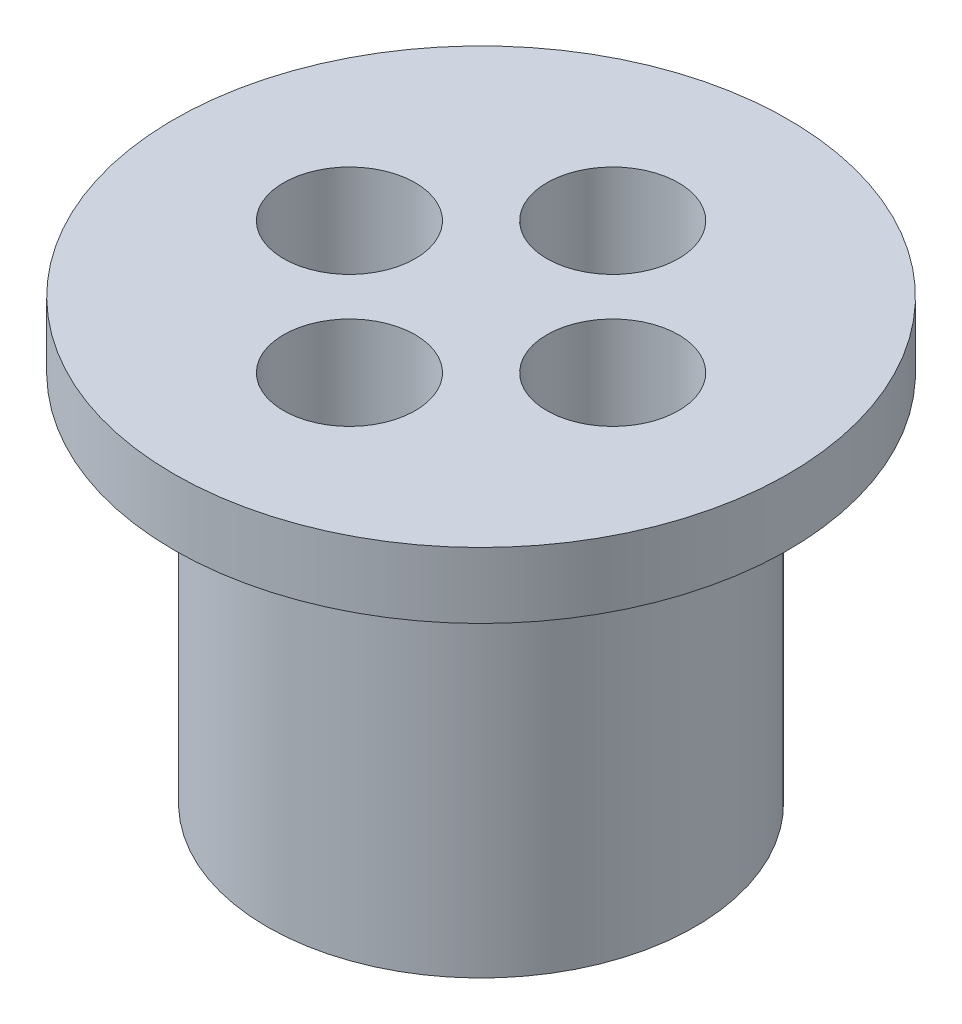
SolidWorks part; units mm, degrees
ref_plane "Front Plane" through (0, 0, 0) normal (0, 0, 1) x (1, 0, 0)
ref_plane "Top Plane" through (0, 0, 0) normal (0, 1, 0) x (1, 0, 0)
ref_plane "Right Plane" through (0, 0, 0) normal (1, 0, 0) x (0, 0, -1)
sketch "Sketch1" plane through (0, 0, 0) normal (0, 1, 0) x (1, 0, 0)
  circle A0 centre (0, 0) radius 9.75
  dimension "D1" = 19.5
extrude "Boss-Extrude1" add sketch "Sketch1" along normal blind 17
sketch "Sketch2" plane through (0, 17, 0) normal (0, 1, 0) x (1, 0, 0)
  circle A0 centre (0, 0) radius 14
extrude "Boss-Extrude2" add sketch "Sketch2" along normal blind 3
sketch "Sketch3" plane through (0, 0, 0) normal (0, -1, 0) x (1, 0, 0)
  circle A0 centre (0, 6) radius 1.75
  dimension "D1" = 3.5
  dimension "D2" = 6
extrude "Cut-Extrude1" cut sketch "Sketch3" against normal through all
pattern_circular "CirPattern1" count 4 every 90 about axis through (0, 0, 0) along (0, 1, 0) of "Cut-Extrude1"
sketch "Sketch4" plane through (0, 20, 0) normal (0, 1, 0) x (1, 0, 0)
  circle A0 centre (0, 6) radius 3
extrude "Cut-Extrude2" cut sketch "Sketch4" against normal blind 10
pattern_circular "CirPattern2" count 4 every 90 about axis through (0, 0, 0) along (0, 1, 0) of "Cut-Extrude2"
